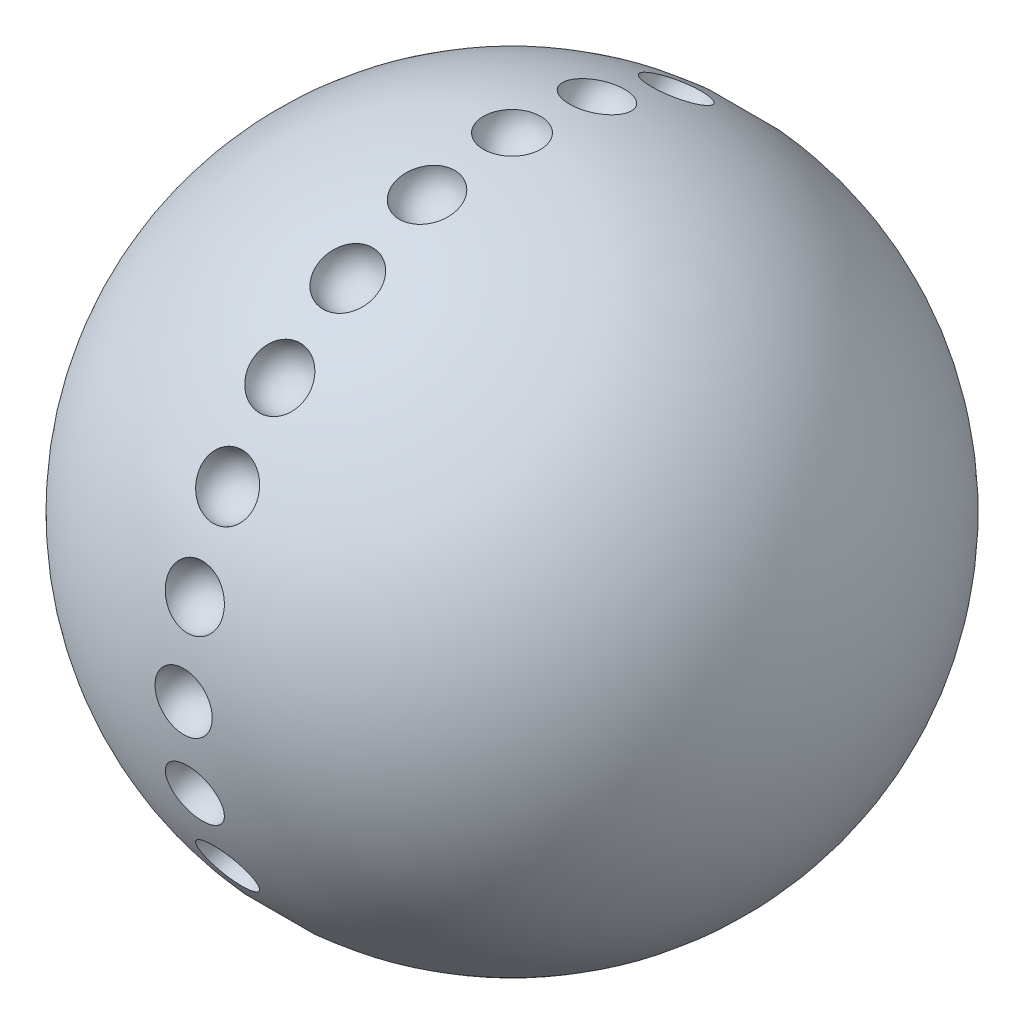
SolidWorks part; units mm, degrees
ref_plane "Front Plane" through (0, 0, 0) normal (0, 0, 1) x (1, 0, 0)
ref_plane "Top Plane" through (0, 0, 0) normal (0, 1, 0) x (1, 0, 0)
ref_plane "Right Plane" through (0, 0, 0) normal (1, 0, 0) x (0, 0, -1)
sketch "Sketch1" plane through (0, 0, 0) normal (0, 0, 1) x (1, 0, 0)
  line L0 (0, 77.4494) -> (0, -77.4494)
  arc A0 (0, -77.4494) -> (0, 77.4494) centre (0, 0) ccw
revolve "Revolve1" add sketch "Sketch1" angle 360 about L0
sketch "Sketch2" plane through (0, 0, 0) normal (0, 1, 0) x (1, 0, 0)
  line L0 (-6.7331, 77.4494) -> (6.7331, 77.4494)
  arc A0 (-6.7331, 77.4494) -> (6.7331, 77.4494) centre (0, 77.4494) ccw
  circle A1 centre (0, 0) radius 77.4494 construction
revolve "Cut-Revolve1" cut sketch "Sketch2" angle 360 about L0
sketch "Sketch3" plane through (0, 0, 0) normal (0, 1, 0) x (1, 0, 0)
  line L0 (-84.7522, 0) -> (85.0673, 0) construction
pattern_circular "CirPattern1" count 24 every 15 about axis through (0, 0, 0) along (1, 0, 0) of "Cut-Revolve1"
